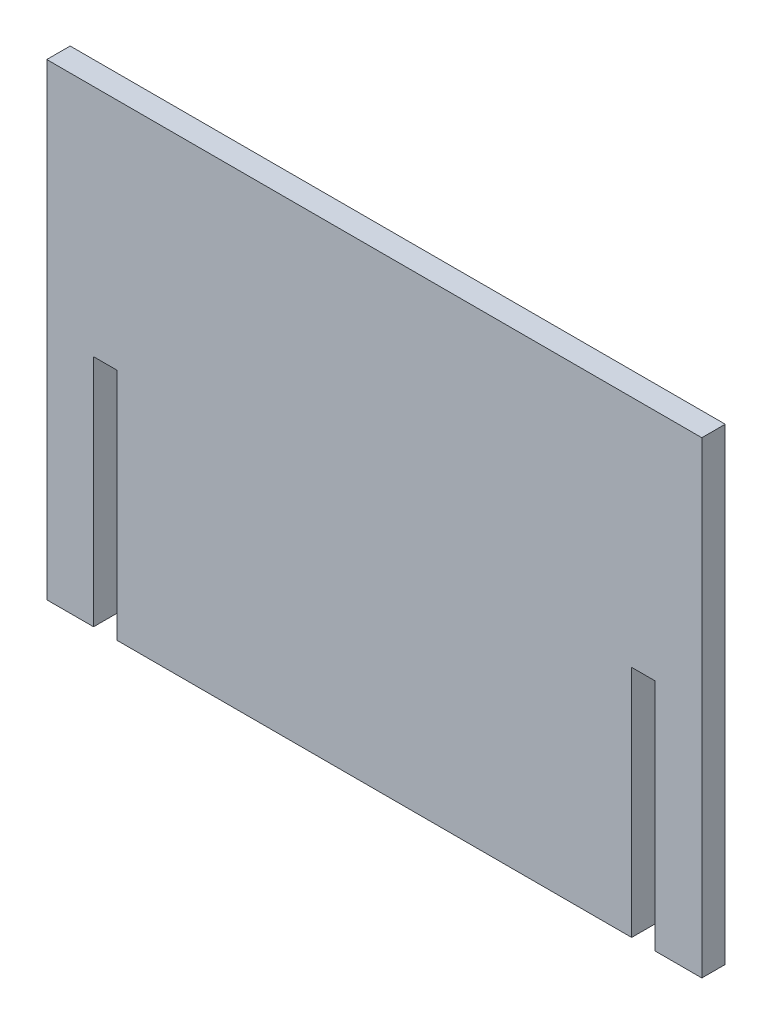
SolidWorks part; units mm, degrees
ref_plane "Front Plane" through (0, 0, 0) normal (0, 0, 1) x (1, 0, 0)
ref_plane "Top Plane" through (0, 0, 0) normal (0, 1, 0) x (1, 0, 0)
ref_plane "Right Plane" through (0, 0, 0) normal (1, 0, 0) x (0, 0, -1)
sketch "Sketch1" plane through (0, 0, 0) normal (0, 0, 1) x (1, 0, 0)
  line L7 (1294.204, -519.4799) -> (1294.204, -532.1799) construction
  line L8 (1294.204, -24.1799) -> (1649.804, -24.1799)
  line L9 (1294.204, -24.1799) -> (1294.204, -278.1799)
  line L11 (1649.804, -24.1799) -> (1649.804, -278.1799)
  line L12 (1649.804, -519.4799) -> (1649.804, -532.1799) construction
  line L13 (1332.304, -24.1799) -> (1319.604, -24.1799) construction
  line L14 (1294.204, -278.1799) -> (1319.604, -278.1799)
  line L15 (1319.604, -24.1799) -> (1319.604, -519.4799) construction
  line L16 (1319.604, -278.1799) -> (1319.604, -151.1799)
  line L17 (1319.604, -151.1799) -> (1332.304, -151.1799)
  line L18 (1332.304, -24.1799) -> (1332.304, -519.4799) construction
  line L19 (1332.304, -151.1799) -> (1332.304, -278.1799)
  line L20 (1332.304, -278.1799) -> (1611.704, -278.1799)
  line L21 (1611.704, -24.1799) -> (1611.704, -519.4799) construction
  line L22 (1611.704, -278.1799) -> (1611.704, -151.1799)
  line L23 (1611.704, -151.1799) -> (1624.404, -151.1799)
  line L24 (1624.404, -24.1799) -> (1624.404, -519.4799) construction
  line L25 (1624.404, -151.1799) -> (1624.404, -278.1799)
  line L26 (1624.404, -278.1799) -> (1649.804, -278.1799)
  point P21 (0, 0)
  dimension "D1" = 127
  dimension "D2" = 254
extrude "Boss-Extrude1" add sketch "Sketch1" along normal mid plane 12.7
